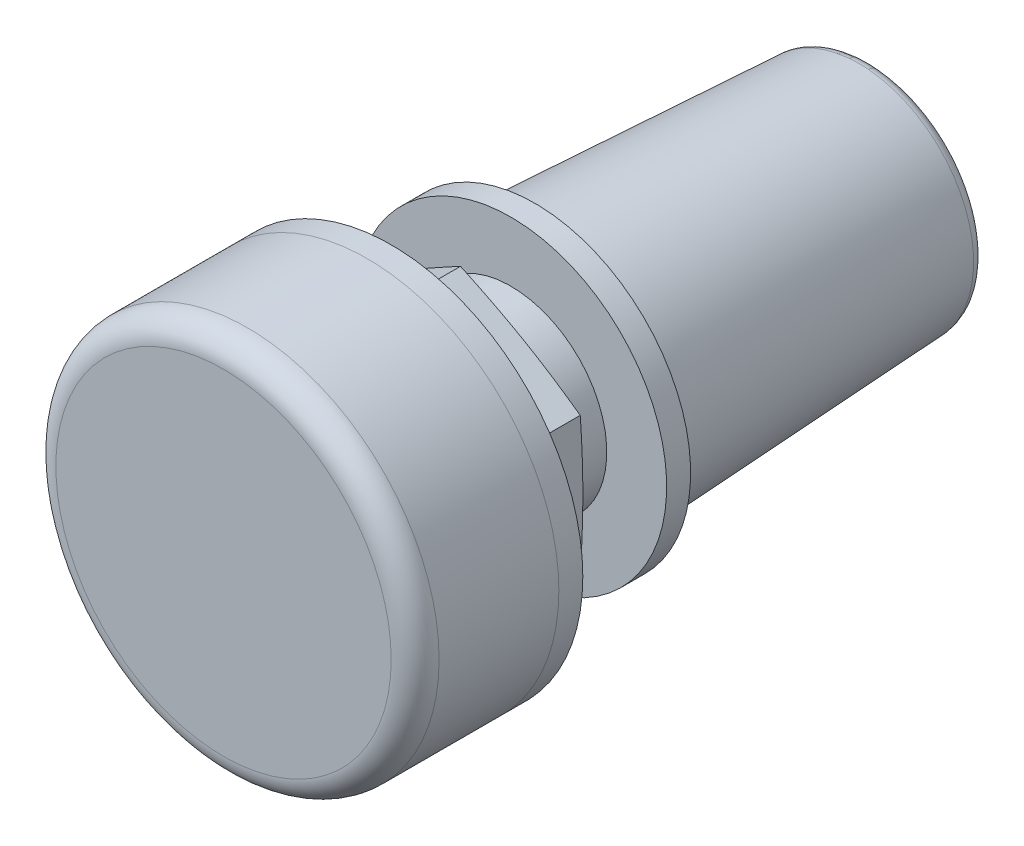
SolidWorks part; units mm, degrees
ref_plane "Face" through (0, 0, 0) normal (0, 0, 1) x (1, 0, 0)
ref_plane "Dessus" through (0, 0, 0) normal (0, 1, 0) x (1, 0, 0)
ref_plane "Droite" through (0, 0, 0) normal (1, 0, 0) x (0, 0, -1)
sketch "Esquisse1" plane through (0, 0, 0) normal (0, 0, 1) x (1, 0, 0)
  circle A0 centre (0, 0) radius 8
  dimension "D1" = 16
extrude "Boss.-Extru.1" add sketch "Esquisse1" along normal blind 6
fillet "Congé1" radius 1 1 edges at (8, 0, 6)
sketch "Esquisse2" plane through (0, 0, 0) normal (0, 0, -1) x (-1, 0, 0)
  circle A1 centre (0, 0) radius 8
  circle A2 centre (0, 0) radius 8
  dimension "D1" = 0
extrude "Boss.-Extru.2" add sketch "Esquisse2" along normal blind 1 separate body
sketch "Esquisse3" plane through (0, 0, -1) normal (0, 0, -1) x (-1, 0, 0)
  circle A0 centre (0, 0) radius 4
  dimension "D1" = 8
extrude "Boss.-Extru.3" add sketch "Esquisse3" along normal blind 5 separate body
cosmetic thread "Représentation de filetage1" parameters "D1"=5, "D2"=7
sketch "Esquisse4" plane through (0, 0, -6) normal (0, 0, -1) x (-1, 0, 0)
  circle A0 centre (0, 0) radius 6.5
  dimension "D1" = 13
extrude "Boss.-Extru.4" add sketch "Esquisse4" along normal blind 1
sketch "Esquisse5" plane through (0, 0, -7) normal (0, 0, -1) x (-1, 0, 0)
  circle A0 centre (0, 0) radius 5.5
  dimension "D1" = 11
extrude "Boss.-Extru.5" add sketch "Esquisse5" along normal blind 14 draft 3
fillet "Congé2" radius 0.5 1 edges at (-4.7663, 0, -21)
sketch "Esquisse6" plane through (0, 0, -21) normal (0, 0, -1) x (-1, 0, 0)
  line L0 (-0.4, 1.2744) -> (0.4, 1.2744)
  line L1 (0.4, 1.2744) -> (0.4, 4.7744)
  line L2 (-0.4, 1.2744) -> (-0.4, 4.7744)
  circle A0 centre (0, 0) radius 4.7911 construction
  dimension "D1" = 3.5
  dimension "D2" = 0.8
split line "Ligne de séparation1"
sketch "Esquisse7" plane through (0, 0, -1) normal (0, 0, -1) x (-1, 0, 0)
  line L1 (-5, 2.8868) -> (-5, -2.8868)
  line L2 (-5, -2.8868) -> (0, -5.7735)
  line L3 (0, -5.7735) -> (5, -2.8868)
  line L4 (5, -2.8868) -> (5, 2.8868)
  line L5 (5, 2.8868) -> (0, 5.7735)
  line L6 (0, 5.7735) -> (-5, 2.8868)
  circle A0 centre (0, 0) radius 5 construction
  dimension "D1" = 10
extrude "Boss.-Extru.6" add sketch "Esquisse7" along normal blind 1.5 from offset 1.5 separate body
sketch "Esquisse8" plane through (0, 0, -4) normal (0, 0, -1) x (-1, 0, 0)
  line L0 (5, -2.8868) -> (5, 2.8868) construction
  circle A0 centre (0, 0) radius 5
extrude "Enlèv. mat.-Extru.3" cut sketch "Esquisse8" against normal blind 1.5 draft 82 flip side to cut
sketch "Esquisse9" plane through (0, 0, -2.5) normal (0, 0, 1) x (1, 0, 0)
  line L0 (-5, -2.8868) -> (-5, 2.8868) construction
  circle A0 centre (0, 0) radius 5
extrude "Enlèv. mat.-Extru.4" cut sketch "Esquisse9" against normal blind 1.5 draft 82 flip side to cut
